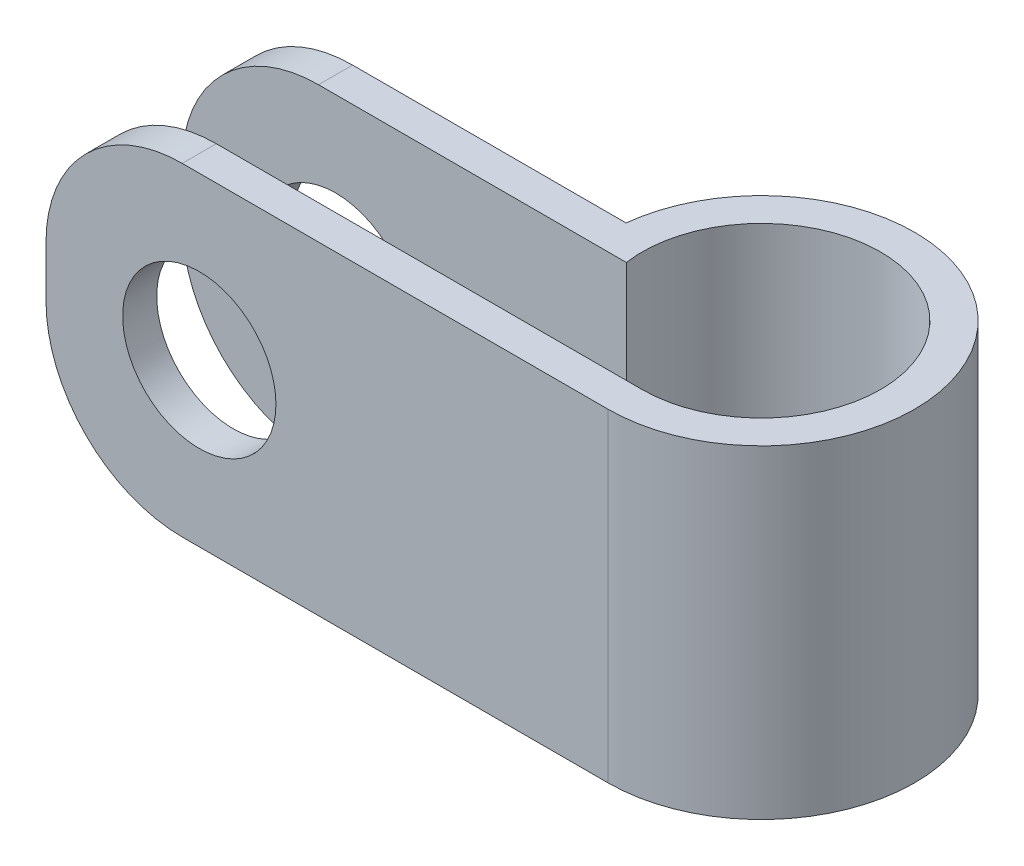
SolidWorks part; units mm, degrees
ref_plane "Front Plane" through (0, 0, 0) normal (0, 0, 1) x (1, 0, 0)
ref_plane "Top Plane" through (0, 0, 0) normal (0, 1, 0) x (1, 0, 0)
ref_plane "Right Plane" through (0, 0, 0) normal (1, 0, 0) x (0, 0, -1)
sketch "Sketch1" plane through (0, 0, 0) normal (0, 1, 0) x (1, 0, 0)
  line L0 (0, -3.5) -> (-16.5, -3.5)
  line L1 (-3.4641, -0.5) -> (-16.5, -0.5)
  line L2 (-16.5, -0.5) -> (-16.5, 0.5)
  line L3 (-16.5, 0.5) -> (-4.4721, 0.5)
  line L4 (-16.5, -3.5) -> (-16.5, -4.5)
  line L5 (-16.5, -4.5) -> (0, -4.5)
  circle A0 centre (0, 0) radius 3.5 construction
  arc A1 (0, -4.5) -> (-4.4721, 0.5) centre (0, 0) ccw
  arc A2 (-3.4641, -0.5) -> (0, -3.5) centre (0, 0) cw
  dimension "D1" = 7
  dimension "D2" = 1
  dimension "D3" = 1
  dimension "D4" = 3
  dimension "D5" = 16.5
extrude "Boss-Extrude1" add sketch "Sketch1" along normal mid plane 9.5
sketch "Sketch2" plane through (0, 0, 4.5) normal (0, 0, 1) x (1, 0, 0)
  line L0 (-16.5, 4.75) -> (-16.5, -4.75) construction
  circle A0 centre (-12, 0) radius 2.25
  dimension "D1" = 4.5
  dimension "D2" = 4.5
extrude "Cut-Extrude1" cut sketch "Sketch2" against normal through all contours A0
fillet "Fillet1" radius 4 4 edges at (-16.5, -4.75, 0) (-16.5, 4.75, 0) (-16.5, -4.75, 4) (-16.5, 4.75, 4)
